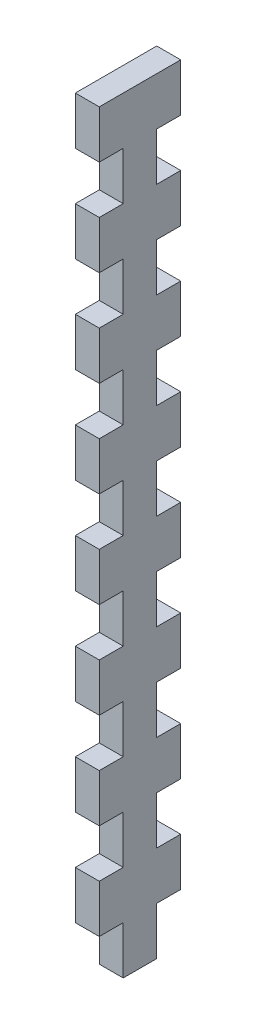
SolidWorks part; units mm, degrees
material "Balsa"
ref_plane "Alzado" through (0, 0, 0) normal (0, 0, 1) x (1, 0, 0)
ref_plane "Planta" through (0, 0, 0) normal (0, 1, 0) x (1, 0, 0)
ref_plane "Vista lateral" through (0, 0, 0) normal (1, 0, 0) x (0, 0, -1)
sketch "Croquis1" plane through (0, 0, 0) normal (1, 0, 0) x (0, 0, -1)
  line L0 (-17.1505, 62.7891) -> (-17.1505, 52.7891)
  line L1 (-17.1505, 92.7891) -> (-0.1505, 92.7891)
  line L2 (-17.1505, 92.7891) -> (-17.1505, -67.2109)
  line L3 (-17.1505, -67.2109) -> (-0.1505, -67.2109)
  line L4 (-0.1505, 92.7891) -> (-0.1505, -67.2109)
  line L5 (-17.1505, 82.7891) -> (-12.1505, 82.7891)
  line L6 (-17.1505, 82.7891) -> (-17.1505, 72.7891)
  line L7 (-17.1505, 72.7891) -> (-12.1505, 72.7891)
  line L8 (-12.1505, 82.7891) -> (-12.1505, 72.7891)
  line L9 (-17.1505, 62.7891) -> (-12.1505, 62.7891)
  line L10 (-12.1505, 62.7891) -> (-12.1505, 52.7891)
  line L11 (-17.1505, 52.7891) -> (-12.1505, 52.7891)
  line L12 (-17.1505, 42.7891) -> (-17.1505, 32.7891)
  line L13 (-17.1505, 42.7891) -> (-12.1505, 42.7891)
  line L14 (-12.1505, 42.7891) -> (-12.1505, 32.7891)
  line L15 (-17.1505, 32.7891) -> (-12.1505, 32.7891)
  line L16 (-17.1505, 22.7891) -> (-17.1505, 12.7891)
  line L17 (-17.1505, 22.7891) -> (-12.1505, 22.7891)
  line L18 (-12.1505, 22.7891) -> (-12.1505, 12.7891)
  line L19 (-17.1505, 12.7891) -> (-12.1505, 12.7891)
  line L20 (-17.1505, 2.7891) -> (-17.1505, -7.2109)
  line L21 (-17.1505, 2.7891) -> (-12.1505, 2.7891)
  line L22 (-12.1505, 2.7891) -> (-12.1505, -7.2109)
  line L23 (-17.1505, -7.2109) -> (-12.1505, -7.2109)
  line L24 (-17.1505, -17.2109) -> (-17.1505, -27.2109)
  line L25 (-17.1505, -17.2109) -> (-12.1505, -17.2109)
  line L26 (-12.1505, -17.2109) -> (-12.1505, -27.2109)
  line L27 (-17.1505, -27.2109) -> (-12.1505, -27.2109)
  line L28 (-17.1505, -37.2109) -> (-17.1505, -47.2109)
  line L29 (-17.1505, -37.2109) -> (-12.1505, -37.2109)
  line L30 (-12.1505, -37.2109) -> (-12.1505, -47.2109)
  line L31 (-17.1505, -47.2109) -> (-12.1505, -47.2109)
  line L32 (-17.1505, -57.2109) -> (-17.1505, -67.2109)
  line L33 (-17.1505, -57.2109) -> (-12.1505, -57.2109)
  line L34 (-12.1505, -57.2109) -> (-12.1505, -67.2109)
  line L35 (-17.1505, -67.2109) -> (-12.1505, -67.2109)
  line L37 (-0.1505, 72.7891) -> (-5.1505, 72.7891)
  line L38 (-5.1505, 82.7891) -> (-5.1505, 72.7891)
  line L39 (-0.1505, 82.7891) -> (-5.1505, 82.7891)
  line L40 (-0.1505, 82.7891) -> (-0.1505, 72.7891)
  line L41 (-0.1505, 62.7891) -> (-5.1505, 62.7891)
  line L42 (-5.1505, 62.7891) -> (-5.1505, 52.7891)
  line L43 (-0.1505, 52.7891) -> (-5.1505, 52.7891)
  line L44 (-0.1505, 62.7891) -> (-0.1505, 52.7891)
  line L45 (-0.1505, 42.7891) -> (-5.1505, 42.7891)
  line L46 (-5.1505, 42.7891) -> (-5.1505, 32.7891)
  line L47 (-0.1505, 32.7891) -> (-5.1505, 32.7891)
  line L48 (-0.1505, 42.7891) -> (-0.1505, 32.7891)
  line L49 (-0.1505, 22.7891) -> (-5.1505, 22.7891)
  line L50 (-5.1505, 22.7891) -> (-5.1505, 12.7891)
  line L51 (-0.1505, 12.7891) -> (-5.1505, 12.7891)
  line L52 (-0.1505, 22.7891) -> (-0.1505, 12.7891)
  line L53 (-0.1505, 2.7891) -> (-5.1505, 2.7891)
  line L54 (-5.1505, 2.7891) -> (-5.1505, -7.2109)
  line L55 (-0.1505, -7.2109) -> (-5.1505, -7.2109)
  line L56 (-0.1505, 2.7891) -> (-0.1505, -7.2109)
  line L57 (-0.1505, -17.2109) -> (-5.1505, -17.2109)
  line L58 (-5.1505, -17.2109) -> (-5.1505, -27.2109)
  line L59 (-0.1505, -27.2109) -> (-5.1505, -27.2109)
  line L60 (-0.1505, -17.2109) -> (-0.1505, -27.2109)
  line L61 (-0.1505, -37.2109) -> (-5.1505, -37.2109)
  line L62 (-5.1505, -37.2109) -> (-5.1505, -47.2109)
  line L63 (-0.1505, -47.2109) -> (-5.1505, -47.2109)
  line L64 (-0.1505, -37.2109) -> (-0.1505, -47.2109)
  line L65 (-0.1505, -57.2109) -> (-5.1505, -57.2109)
  line L66 (-5.1505, -57.2109) -> (-5.1505, -67.2109)
  line L67 (-0.1505, -67.2109) -> (-5.1505, -67.2109)
  line L68 (-0.1505, -57.2109) -> (-0.1505, -67.2109)
  dimension "D1" = 160
  dimension "D2" = 17
  dimension "D3" = 10
  dimension "D4" = 10
  dimension "D5" = 5
  dimension "D6" = 8
extrude "Saliente-Extruir1" add sketch "Croquis1" along normal blind 5 contours L66 L65 L4 L63 L62 L61 L59 L58 L57 L55 L54 L53 L51 L50 L49 L47 L46 L45 L43 L42 L41 L37 L38 L39 L1 L2 L5 L8 L7 L9 L10 L11 L13 L14 L15 L17 L18 L19 L21 L22
